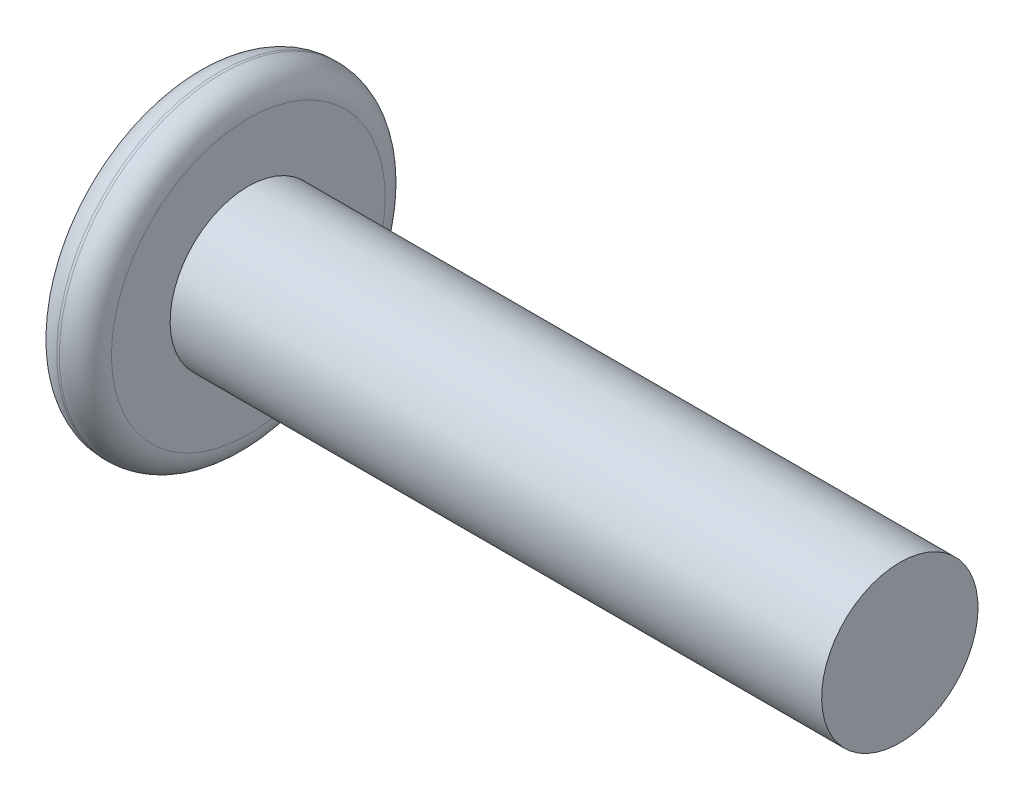
SolidWorks part; units mm, degrees
material "AISI 304"
ref_plane "前视基准面" through (0, 0, 0) normal (0, 0, 1) x (1, 0, 0)
ref_plane "上视基准面" through (0, 0, 0) normal (0, 1, 0) x (1, 0, 0)
ref_plane "右视基准面" through (0, 0, 0) normal (1, 0, 0) x (0, 0, -1)
sketch "草图1" plane through (0, 0, 0) normal (0, 0, 1) x (1, 0, 0)
  line L0 (0, 0) -> (0, 6.25)
  line L1 (0, 6.25) -> (2.1, 6.25)
  line L2 (2.1, 6.25) -> (2.1, 3)
  line L3 (2.1, 3) -> (27.1, 3)
  line L4 (27.1, 3) -> (27.1, 0)
  line L5 (27.1, 0) -> (0, 0)
  dimension "D1" = 6.25
  dimension "D2" = 2.1
  dimension "D3" = 25
  dimension "D4" = 3
revolve "旋转1" add sketch "草图1" angle 360 about L5
cosmetic thread "装饰螺纹线1" parameters "D2"=4.917
fillet "圆角1" radius 1 2 edges at (2.1, 6.25, 0) (0, 6.25, 0)
sketch "草图2" plane through (0, 0, 0) normal (-1, 0, 0) x (0, 0, 1)
  line L1 (1.1547, 2) -> (-1.1547, 2)
  line L2 (-1.1547, 2) -> (-2.3094, 0)
  line L3 (-2.3094, 0) -> (-1.1547, -2)
  line L4 (-1.1547, -2) -> (1.1547, -2)
  line L5 (1.1547, -2) -> (2.3094, 0)
  line L6 (2.3094, 0) -> (1.1547, 2)
  circle A0 centre (0, 0) radius 2 construction
  dimension "D1" = 4
extrude "切除-拉伸1" cut sketch "草图2" against normal blind 1
